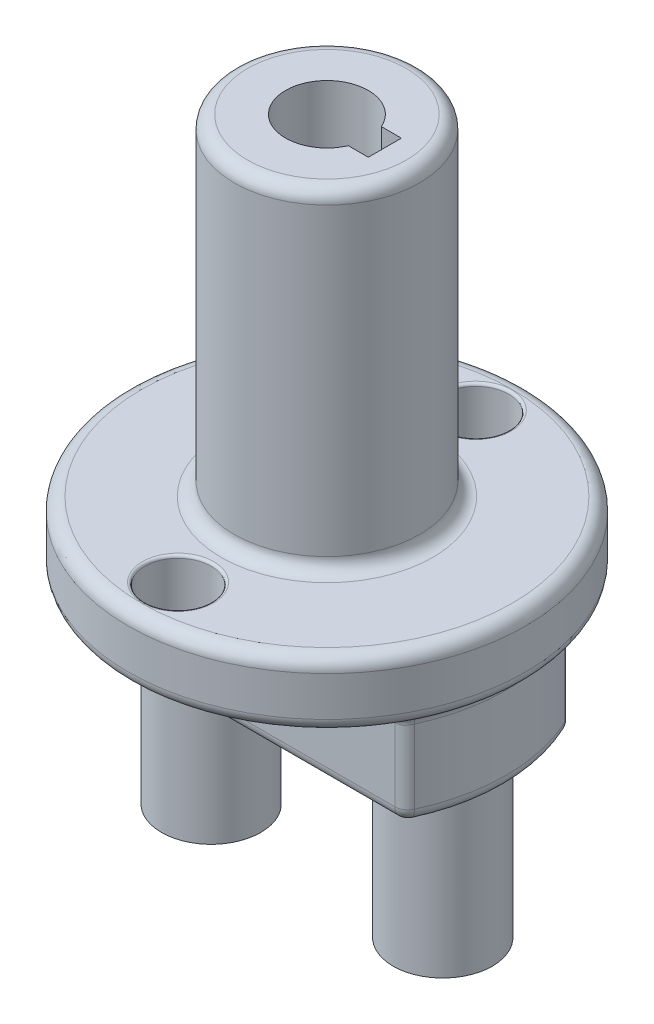
SolidWorks part; units mm, degrees
ref_plane "Front Plane" through (0, 0, 0) normal (0, 0, 1) x (1, 0, 0)
ref_plane "Top Plane" through (0, 0, 0) normal (0, 1, 0) x (1, 0, 0)
ref_plane "Right Plane" through (0, 0, 0) normal (1, 0, 0) x (0, 0, -1)
sketch "Sketch1" plane through (0, 0, 0) normal (0, 1, 0) x (1, 0, 0)
  circle A0 centre (0, 0) radius 19.05
  dimension "D1" = 38.1
extrude "Extrude1" add sketch "Sketch1" along normal blind 6.35
sketch "Sketch2" plane through (0, 0, 0) normal (0, -1, 0) x (1, 0, 0)
  line L0 (-15.24, 7.9375) -> (15.24, 7.9375)
  line L1 (15.24, -7.9375) -> (-15.24, -7.9375)
  arc A0 (15.24, -7.9375) -> (15.24, 7.9375) centre (0, 0) ccw
  arc A1 (-15.24, -7.9375) -> (-15.24, 7.9375) centre (0, 0) cw
  circle A3 centre (0, 0) radius 19.05 construction
  dimension "D1" = 15.875
  dimension "D2" = 7.9375
  dimension "D3" = 15.24
  dimension "D4" = 15.24
extrude "Extrude2" add sketch "Sketch2" along normal blind 9.525
sketch "Sketch3" plane through (0, 6.35, 0) normal (0, 1, 0) x (-1, 0, 0)
  circle A0 centre (0, 0) radius 8.89
  dimension "D1" = 17.78
extrude "Extrude3" add sketch "Sketch3" along normal blind 31.75
sketch "Sketch4" plane through (0, 38.1, 0) normal (0, 1, 0) x (-1, 0, 0)
  circle A0 centre (0, 0) radius 3.9688
  dimension "D1" = 7.9375
extrude "Cut-Extrude1" cut sketch "Sketch4" against normal blind 25.4
sketch "Sketch5" plane through (0, -9.525, 0) normal (0, -1, 0) x (1, 0, 0)
  line L0 (15.24, 7.9375) -> (-15.24, 7.9375) construction
  circle A0 centre (11.1125, 0) radius 4.7625
  circle A1 centre (-11.1125, 0) radius 4.7625
  dimension "D1" = 9.525
  dimension "D2" = 9.525
  dimension "D3" = 22.225
  dimension "D4" = 11.1125
  dimension "D5" = 7.9375
extrude "Extrude4" add sketch "Sketch5" along normal blind 15.24
sketch "Sketch6" plane through (0, 38.1, 0) normal (0, 1, 0) x (-1, 0, 0)
  line L1 (-2.3812, -1.5875) -> (-5.5562, -1.5875)
  line L2 (-2.3812, -1.5875) -> (-2.3812, 1.5875)
  line L3 (-2.3812, 1.5875) -> (-5.5562, 1.5875)
  line L4 (-5.5562, -1.5875) -> (-5.5562, 1.5875)
  dimension "D1" = 3.175
  dimension "D2" = 3.175
  dimension "D3" = 1.5875
  dimension "D4" = 5.5562
extrude "Cut-Extrude2" cut sketch "Sketch6" against normal up to surface (25.4 mm away) up to face at (0, 12.7, 3.9688)
fillet "Fillet1" radius 1.27 12 edges at (17.1832, -9.525, 0) (0, -9.525, 7.9375) (-17.1832, -9.525, 0) (0, -9.525, -7.9375) (-15.24, -4.7625, -7.9375) (15.24, -4.7625, -7.9375) (15.24, -4.7625, 7.9375) (-15.24, -4.7625, 7.9375) (0, 0, 19.05) (0, 6.35, 19.05) (0, 6.35, 8.89) (0, 38.1, 8.89)
fillet "Fillet2" radius 1.27 8 edges at (-15.1335, 0, -7.7372) (-17.1832, 0, 0) (-15.1335, 0, 7.7372) (0, 0, 7.9375) (15.1335, 0, 7.7372) (17.1832, 0, 0) (15.1335, 0, -7.7372) (0, 0, -7.9375)
sketch "Sketch7" plane through (0, 6.35, 0) normal (0, 1, 0) x (-1, 0, 0)
  circle A0 centre (0, 14.2875) radius 3.175
  circle A1 centre (0, -14.2875) radius 3.175
  dimension "D1" = 6.35
  dimension "D2" = 6.35
  dimension "D3" = 28.575
  dimension "D4" = 14.2875
extrude "Cut-Extrude3" cut sketch "Sketch7" against normal through all
fillet "Fillet3" radius 0.254 4 edges at (0, 6.35, -11.1125) (0, 6.35, 17.4625) (0, 0, 17.4625) (0, 0, -11.1125)
